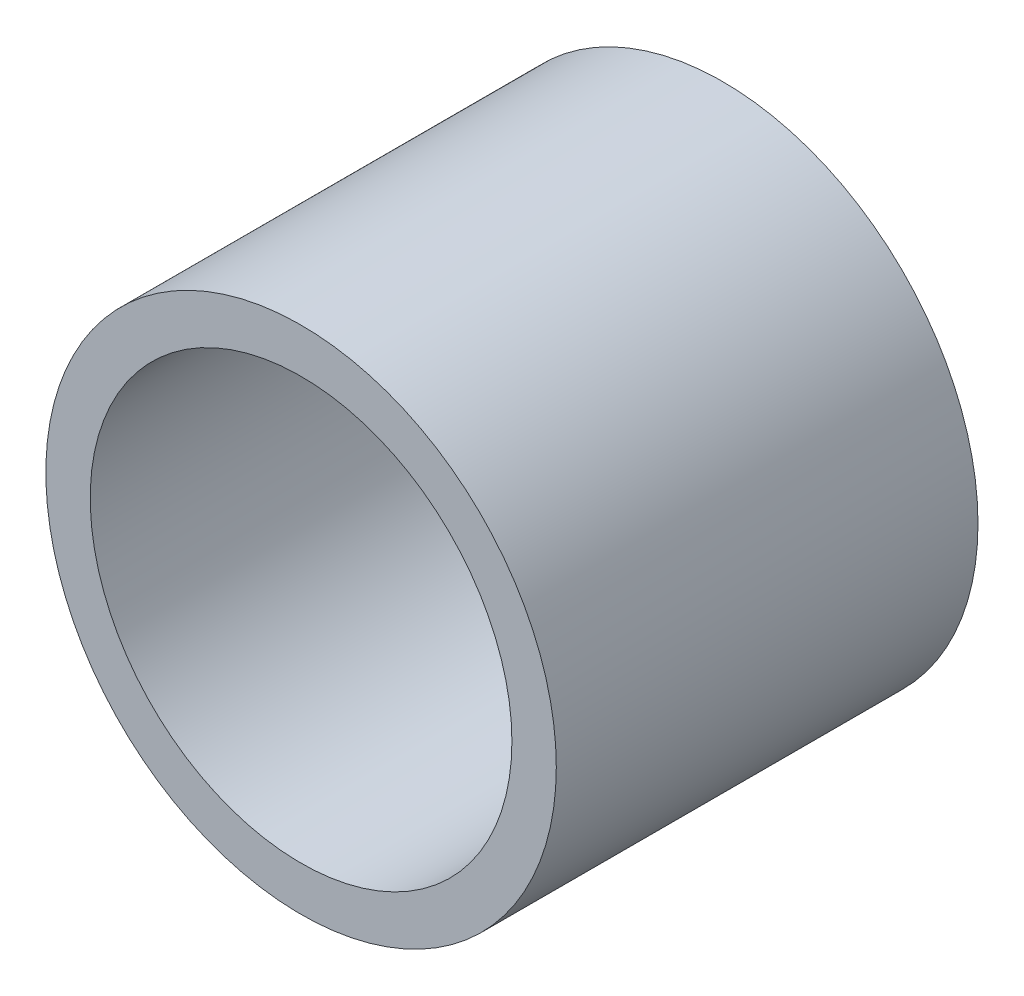
SolidWorks part; units mm, degrees
ref_plane "Alzado" through (0, 0, 0) normal (0, 0, 1) x (1, 0, 0)
ref_plane "Planta" through (0, 0, 0) normal (0, 1, 0) x (1, 0, 0)
ref_plane "Vista lateral" through (0, 0, 0) normal (1, 0, 0) x (0, 0, -1)
sketch "Croquis1" plane through (0, 0, 0) normal (0, 0, 1) x (1, 0, 0)
  circle A0 centre (0, 0) radius 9.5
  circle A1 centre (0, 0) radius 11.5
  dimension "D1" = 19
  dimension "D2" = 23
extrude "Saliente-Extruir1" add sketch "Croquis1" against normal blind 19
